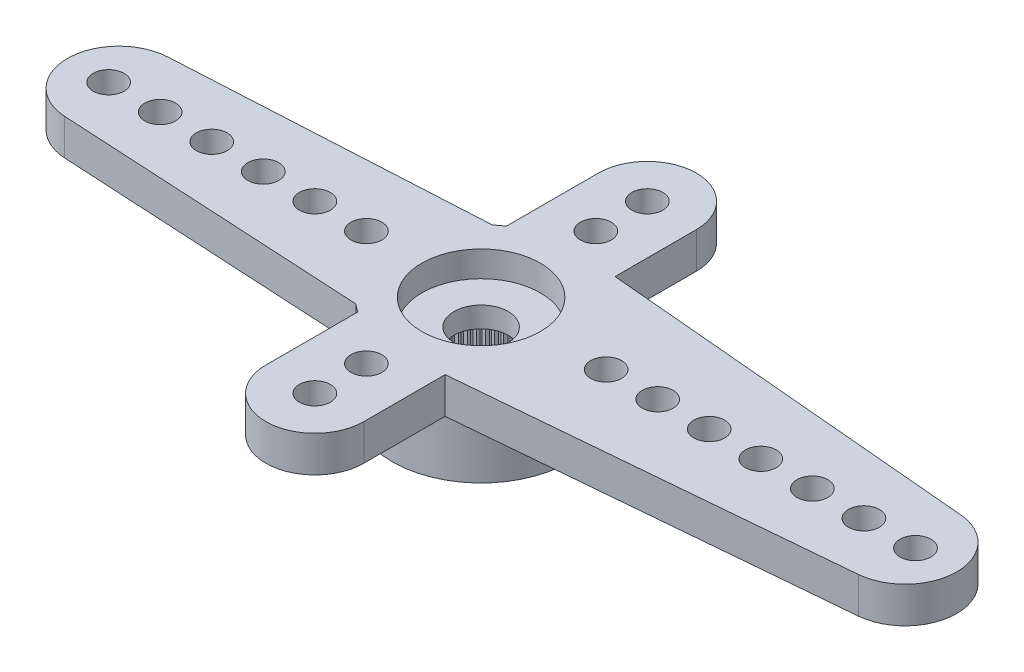
SolidWorks part; units mm, degrees
material "PVC Rígido"
ref_plane "Plano frontal" through (0, 0, 0) normal (0, 0, 1) x (1, 0, 0)
ref_plane "Plano superior" through (0, 0, 0) normal (0, 1, 0) x (1, 0, 0)
ref_plane "Plano direito" through (0, 0, 0) normal (1, 0, 0) x (0, 0, -1)
sketch "Esboço1" plane through (0, 0, 0) normal (0, 1, 0) x (1, 0, 0)
  line L0 (0, 0) -> (-14.05, 0) construction
  line L1 (-14.1591, 1.997) -> (-2.2091, 2.65)
  line L2 (-2.2091, -2.65) -> (-14.1591, -1.997)
  arc A0 (-2.2091, -2.65) -> (-2.2091, 2.65) centre (0, 0) ccw
  arc A1 (-14.1591, 1.997) -> (-14.1591, -1.997) centre (-14.05, 0) ccw
  dimension "D1" = 6.9
  dimension "D2" = 4
  dimension "D3" = 19.5
  dimension "D4" = 5.3
extrude "Ressalto-extrusão1" add sketch "Esboço1" against normal blind 1.4
sketch "Esboço2" plane through (0, -1.4, 0) normal (0, -1, 0) x (1, 0, 0)
  arc A0 (-2.2091, -2.65) -> (-2.2091, 2.65) centre (0, 0) ccw construction
  circle A1 centre (0, 0) radius 3.45
extrude "Ressalto-extrusão2" add sketch "Esboço2" along normal offset from surface (2.4 mm away) 3.8 up to face at (-7.242, 0, 0)
hole_wizard "Furo1" positions "Esboço9" profile "Esboço10" legacy end condition through all
sketch "Esboço9" plane through (0, 0, 0) normal (0, 1, 0) x (1, 0, 0)
  line L1 (-14.45, 0) -> (0, 0) construction
  arc A2 (-14.1591, 1.997) -> (-14.1591, -1.997) centre (-14.05, 0) ccw construction
  point P0 (-14.45, 0)
  point P19 (-16.05, 0)
  dimension "D1" = 1.6
sketch "Esboço10" plane through (-14.45, 0, 0) normal (1, 0, 0) x (0, 0, 1)
  line L0 (0, 0) -> (0, 3.8)
  line L1 (0, 3.8) -> (0.6, 3.8)
  line L2 (0.6, 3.8) -> (0.6, 0)
  line L3 (0.6, 0) -> (0, 0)
  line L4 (0, 110) -> (0, -10) construction
  dimension "Diameter" = 1.2
  dimension "Depth" = 3.8
pattern_linear "Padrão linear1" count 6 spacing 2 along (1, 0, 0) of "Furo1"
sketch "Esboço12" plane through (0, 0, 0) normal (0, 1, 0) x (1, 0, 0)
  line L0 (0.3041, 3.4366) -> (16.6263, 1.9922)
  line L1 (16.6263, -1.9922) -> (0.3041, -3.4366)
  arc A0 (-2.2091, -2.65) -> (-2.2091, 2.65) centre (0, 0) ccw construction
  arc A1 (0.3041, -3.4366) -> (0.3041, 3.4366) centre (0, 0) ccw
  arc A2 (16.6263, 1.9922) -> (16.6263, -1.9922) centre (16.45, 0) cw
  arc A3 (-14.1591, 1.997) -> (-14.1591, -1.997) centre (-14.05, 0) ccw construction
  dimension "D1" = 2
  dimension "D2" = 34.5
extrude "Ressalto-extrusão3" add sketch "Esboço12" against normal up to surface (1.4 mm away) up to face at (-12.45, -1.4, 0.6)
hole_wizard "Furo2" positions "Esboço13" profile "Esboço14" legacy end condition through all
sketch "Esboço13" plane through (0, 0, 0) normal (0, 1, 0) x (1, 0, 0)
  line L0 (0, 0) -> (16.85, 0) construction
  arc A0 (16.6263, -1.9922) -> (16.6263, 1.9922) centre (16.45, 0) ccw construction
  point P0 (16.85, 0)
  point P6 (18.45, 0)
  dimension "D1" = 1.6
sketch "Esboço14" plane through (16.85, 0, 0) normal (1, 0, 0) x (0, 0, 1)
  line L0 (0, 0) -> (0, 3.8)
  line L1 (0, 3.8) -> (0.6, 3.8)
  line L2 (0.6, 3.8) -> (0.6, 0)
  line L3 (0.6, 0) -> (0, 0)
  line L4 (0, 110) -> (0, -10) construction
  dimension "Diameter" = 1.2
  dimension "Depth" = 3.8
pattern_linear "Padrão linear2" count 7 spacing 2 along (-1, 0, 0) of "Furo2"
sketch "Esboço16" plane through (0, 0, 0) normal (0, 1, 0) x (1, 0, 0)
  line L0 (0, -6.45) -> (0, 6.45) construction
  line L1 (-1.9, -6.45) -> (-1.9, 6.45)
  line L2 (1.9, -6.45) -> (1.9, 6.45)
  arc A0 (-1.9, -6.45) -> (1.9, -6.45) centre (0, -6.45) ccw
  arc A1 (1.9, 6.45) -> (-1.9, 6.45) centre (0, 6.45) ccw
  point P2 (0, 0)
  dimension "D2" = 16.7
  dimension "D1" = 3.8
extrude "Ressalto-extrusão4" add sketch "Esboço16" against normal up to surface (1.4 mm away) up to face at (14.85, -1.4, 0.6)
hole_wizard "Furo3" positions "Esboço17" profile "Esboço18" legacy end condition through all
sketch "Esboço17" plane through (0, 0, 0) normal (0, 1, 0) x (1, 0, 0)
  point P0 (0, -6.45)
sketch "Esboço18" plane through (0, 0, 6.45) normal (1, 0, 0) x (0, 0, 1)
  line L0 (0, 0) -> (0, 3.8)
  line L1 (0, 3.8) -> (0.6, 3.8)
  line L2 (0.6, 3.8) -> (0.6, 0)
  line L3 (0.6, 0) -> (0, 0)
  line L4 (0, 110) -> (0, -10) construction
  dimension "Diameter" = 1.2
  dimension "Depth" = 3.8
pattern_linear "Padrão linear3" count 2 spacing 2 along (0, 0, -1) of "Furo3"
pattern_circular "PadrãoCircular1" count 2 over 360 about axis through (0, 0, 0) along (0, 1, 0) of "Padrão linear3", "Furo3"
hole_wizard "Furo4" positions "Esboço3" profile "Esboço4" legacy
sketch "Esboço3" plane through (0, -3.8, 0) normal (0, -1, 0) x (-1, 0, 0)
  point P0 (0, 0)
sketch "Esboço4" plane through (0, -3.8, 0) normal (1, 0, 0) x (0, 0, -1)
  line L0 (0, 0) -> (0, 2)
  line L1 (0, 2) -> (2.475, 2)
  line L2 (2.475, 2) -> (2.475, 0)
  line L3 (2.475, 0) -> (0, 0)
  line L4 (0, 110) -> (0, -10) construction
  dimension "Diameter" = 4.95
  dimension "Depth" = 2
hole_wizard "Furo5" positions "Esboço5" profile "Esboço6" legacy
sketch "Esboço5" plane through (0, 0, 0) normal (0, 1, 0) x (1, 0, 0)
  point P0 (0, 0)
sketch "Esboço6" plane through (0, 0, 0) normal (1, 0, 0) x (0, 0, 1)
  line L0 (0, 0) -> (0, 1)
  line L1 (0, 1) -> (2.3, 1)
  line L2 (2.3, 1) -> (2.3, 0)
  line L3 (2.3, 0) -> (0, 0)
  line L4 (0, 110) -> (0, -10) construction
  dimension "Diameter" = 4.6
  dimension "Depth" = 1
hole_wizard "Furo6" positions "Esboço7" profile "Esboço8" legacy end condition through all
sketch "Esboço7" plane through (0, 0, 0) normal (0, 1, 0) x (1, 0, 0)
  point P0 (0, 0)
sketch "Esboço8" plane through (0, 0, 0) normal (1, 0, 0) x (0, 0, 1)
  line L0 (0, 0) -> (0, 3.8)
  line L1 (0, 3.8) -> (1.05, 3.8)
  line L2 (1.05, 3.8) -> (1.05, 0)
  line L3 (1.05, 0) -> (0, 0)
  line L4 (0, 110) -> (0, -10) construction
  dimension "Diameter" = 2.1
  dimension "Depth" = 3.8
sketch "Esboço11" plane through (0, -3.8, 0) normal (0, -1, 0) x (1, 0, 0)
  line L0 (-0.0981, 2.4731) -> (0, 2.375)
  line L1 (0, 2.375) -> (0.0981, 2.4731)
  line L2 (0, 0) -> (0, 2.475) construction
  circle A0 centre (0, 0) radius 2.375 construction
  circle A1 centre (0, 0) radius 2.475
  arc A2 (0.0981, 2.4731) -> (-0.0981, 2.4731) centre (0, 0) ccw
  dimension "D3" = 4.75
  dimension "D2" = 0.1
  dimension "D1" = 0
extrude "Ressalto-extrusão5" add sketch "Esboço11" against normal up to surface (2 mm away) up to face at (0, -1.8, 1.05)
pattern_circular "PadrãoCircular2" count 60 over 360 about axis through (0, 0, 0) along (0, 1, 0) of "Ressalto-extrusão5"
